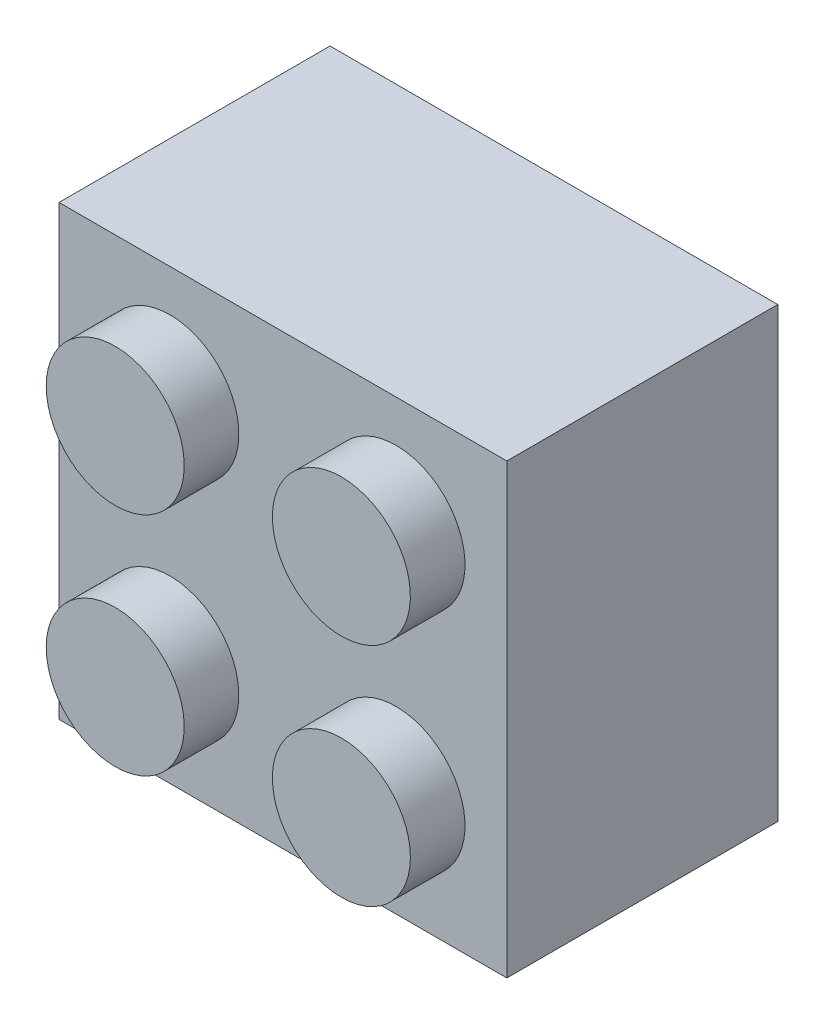
SolidWorks part; units mm, degrees
ref_plane "Front Plane" through (0, 0, 0) normal (0, 0, 1) x (1, 0, 0)
ref_plane "Top Plane" through (0, 0, 0) normal (0, 1, 0) x (1, 0, 0)
ref_plane "Right Plane" through (0, 0, 0) normal (1, 0, 0) x (0, 0, -1)
sketch "Sketch1" plane through (0, 0, 0) normal (0, 0, 1) x (1, 0, 0)
  line L1 (-7.9121, -7.9121) -> (7.9121, -7.9121)
  line L2 (-7.9121, -7.9121) -> (-7.9121, 7.9121)
  line L3 (-7.9121, 7.9121) -> (7.9121, 7.9121)
  line L4 (7.9121, -7.9121) -> (7.9121, 7.9121)
  line L5 (-7.9121, -7.9121) -> (7.9121, 7.9121) construction
  line L6 (-7.9121, 7.9121) -> (7.9121, -7.9121) construction
  point P0 (0, 0)
  dimension "D1" = 15.8242
extrude "Boss-Extrude1" add sketch "Sketch1" along normal blind 9.5758
sketch "Sketch2" plane through (0, 0, 0) normal (0, 0, -1) x (-1, 0, 0)
  line L0 (7.9121, -7.9121) -> (-7.9121, -7.9121) construction
  line L1 (6.7183, 6.7183) -> (-6.7183, 6.7183)
  line L2 (6.7183, 6.7183) -> (6.7183, -6.7183)
  line L3 (6.7183, -6.7183) -> (-6.7183, -6.7183)
  line L4 (-6.7183, 6.7183) -> (-6.7183, -6.7183)
  line L5 (6.7183, 6.7183) -> (-6.7183, -6.7183) construction
  line L6 (6.7183, -6.7183) -> (-6.7183, 6.7183) construction
  circle A0 centre (0, 0) radius 3.2131
  point P0 (0, 0)
  dimension "D2" = 6.4262
  dimension "D1" = 1.1938
extrude "Cut-Extrude1" cut sketch "Sketch2" against normal blind 8.4328
sketch "Sketch3" plane through (0, 0, 0) normal (0, 0, -1) x (-1, 0, 0)
  circle A0 centre (0, 0) radius 2.4384
  dimension "D1" = 4.8768
extrude "Cut-Extrude2" cut sketch "Sketch3" against normal up to surface (8.4328 mm away) up to face at (-3.2131, 0, 8.4328)
sketch "Sketch4" plane through (0, 0, 9.5758) normal (0, 0, 1) x (1, 0, 0)
  line L1 (3.9962, -3.9962) -> (0, 0) construction
  line L3 (3.9962, -3.9962) -> (3.9962, -7.9121) construction
  line L4 (-7.9121, -7.9121) -> (7.9121, -7.9121) construction
  line L5 (3.9962, -3.9962) -> (7.9121, -3.9962) construction
  line L6 (7.9121, -7.9121) -> (7.9121, 7.9121) construction
  circle A0 centre (3.9962, -3.9962) radius 2.4384
  dimension "D1" = 4.8768
  dimension "D2" = 5.6515
extrude "Boss-Extrude2" add sketch "Sketch4" along normal blind 1.9304
pattern_circular "CirPattern1" count 4 over 360 about axis through (0, 0, 0) along (0, 0, 1) of "Boss-Extrude2"
